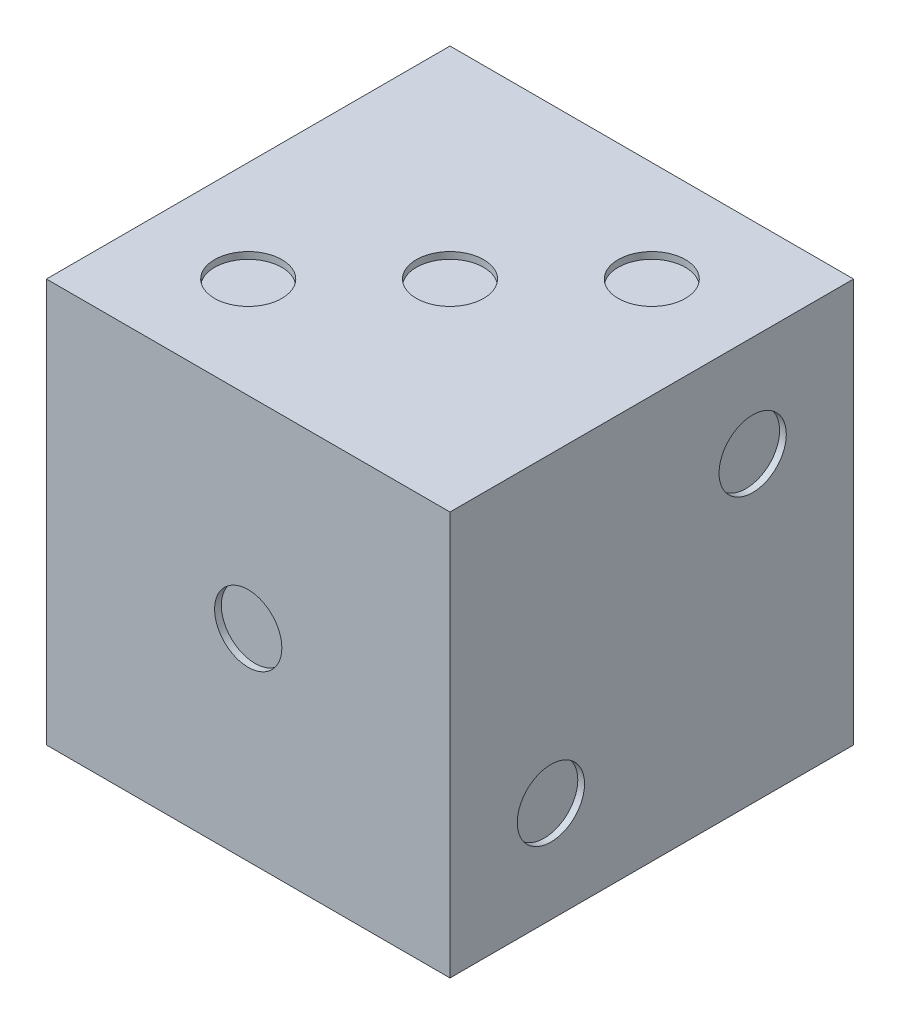
SolidWorks part; units mm, degrees
ref_plane "Front" through (0, 0, 0) normal (0, 0, 1) x (1, 0, 0)
ref_plane "Top" through (0, 0, 0) normal (0, 1, 0) x (1, 0, 0)
ref_plane "Right" through (0, 0, 0) normal (1, 0, 0) x (0, 0, -1)
sketch "Sketch1" plane through (0, 0, 0) normal (0, 1, 0) x (1, 0, 0)
  line L1 (0, 0) -> (60, 0)
  line L2 (0, 0) -> (0, 60)
  line L3 (0, 60) -> (60, 60)
  line L4 (60, 0) -> (60, 60)
  dimension "D1" = 60
  dimension "D2" = 60
extrude "Extrude1" add sketch "Sketch1" along normal blind 60
sketch "Sketch2" plane through (0, 60, 0) normal (0, 1, 0) x (-1, 0, 0)
  circle A0 centre (-45, -45) radius 5
  circle A1 centre (-30, -30) radius 5
  circle A2 centre (-15, -15) radius 5
sketch "Sketch3" plane through (60, 0, 0) normal (1, 0, 0) x (0, 0, -1)
  circle A0 centre (45, 45) radius 5
  circle A1 centre (15, 15) radius 5
sketch "Sketch4" plane through (0, 0, 0) normal (0, 0, 1) x (1, 0, 0)
  circle A0 centre (30, 30) radius 5
sketch "Sketch5" plane through (0, 0, -60) normal (0, 0, -1) x (-1, 0, 0)
  circle A0 centre (-15, 45) radius 5
  circle A1 centre (-15, 30) radius 5
  circle A2 centre (-15, 15) radius 5
  circle A3 centre (-45, 45) radius 5
  circle A4 centre (-45, 30) radius 5
  circle A5 centre (-45, 15) radius 5
sketch "Sketch6" plane through (0, 0, 0) normal (-1, 0, 0) x (0, 0, 1)
  circle A0 centre (-30, 30) radius 5
  circle A1 centre (-45, 45) radius 5
  circle A2 centre (-15, 45) radius 5
  circle A3 centre (-45, 15) radius 5
  circle A4 centre (-15, 15) radius 5
sketch "Sketch7" plane through (0, 0, 0) normal (0, -1, 0) x (1, 0, 0)
  circle A0 centre (15, -45) radius 5
  circle A1 centre (15, -15) radius 5
  circle A2 centre (45, -45) radius 5
  circle A3 centre (45, -15) radius 5
extrude "Cut-Extrude1" cut sketch "Sketch2" against normal blind 1
extrude "Cut-Extrude2" cut sketch "Sketch3" against normal blind 1
extrude "Cut-Extrude3" cut sketch "Sketch4" against normal blind 1
extrude "Cut-Extrude4" cut sketch "Sketch5" against normal blind 1
extrude "Cut-Extrude5" cut sketch "Sketch6" against normal blind 1
extrude "Cut-Extrude6" cut sketch "Sketch7" against normal blind 1
